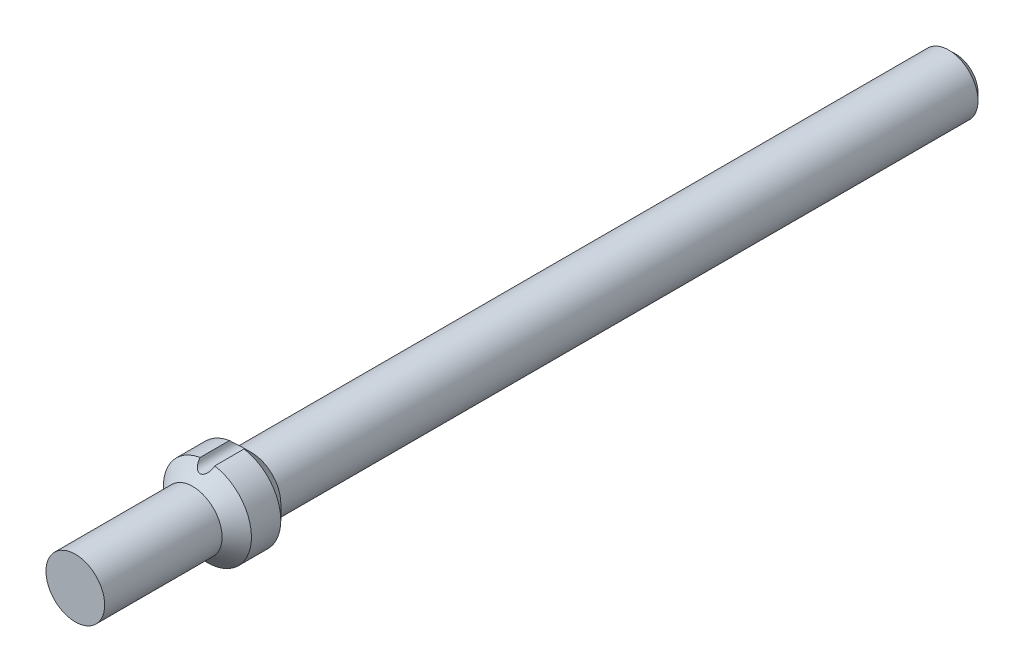
SolidWorks part; units mm, degrees
ref_plane "Front Plane" through (0, 0, 0) normal (0, 0, 1) x (1, 0, 0)
ref_plane "Top Plane" through (0, 0, 0) normal (0, 1, 0) x (1, 0, 0)
ref_plane "Right Plane" through (0, 0, 0) normal (1, 0, 0) x (0, 0, -1)
sketch "Sketch2" plane through (0, 0, 0) normal (0, 1, 0) x (1, 0, 0)
  line L0 (0, -190.5) -> (0, 190.5) construction
  line L1 (0, -190.5) -> (12.7, -190.5)
  line L2 (12.7, -190.5) -> (12.7, -139.7)
  line L3 (12.7, -139.7) -> (19.05, -133.35)
  line L4 (19.05, -133.35) -> (19.05, -120.65)
  line L5 (19.05, -120.65) -> (12.7, -114.3)
  line L6 (12.7, -114.3) -> (12.7, 187.325)
  line L7 (9.525, 190.5) -> (0, 190.5)
  line L8 (12.7, -114.3) -> (12.7, -139.7) construction
  line L9 (12.7, -127) -> (19.05, -127) construction
  line L10 (0, -190.5) -> (0, 190.5)
  line L11 (12.7, 187.325) -> (9.525, 190.5)
  point P3 (0, 0)
  point P10 (12.7, 190.5)
  point P12 (19.05, -125.053)
  dimension "D1" = 381
  dimension "D2" = 12.7
  dimension "D3" = 50.8
  dimension "D4" = 19.05
  dimension "D5" = 135
  dimension "D6" = 12.7
  dimension "D7" = 3.175
  dimension "D8" = 45
revolve "Revolve1" add sketch "Sketch2" angle 360 about L10
sketch "Sketch3" plane through (0, 0, -190.5) normal (0, 0, -1) x (-1, 0, 0)
  circle A0 centre (0, 0) radius 12.7 construction
  circle A1 centre (0, 0) radius 12.7
curve "Helix/Spiral1" [suppressed] pitch 25.4 height 304.8 turns 12
sketch "Sketch4" plane through (0, 0, 190.5) normal (0, 0, 1) x (1, 0, 0)
  circle A0 centre (0, 19.05) radius 3.175
  circle A1 centre (0, 0) radius 19.05 construction
  point P4 (0, 19.05)
  point P5 (0, 0)
  dimension "D1" = 6.35
extrude "Cut-Extrude1" cut sketch "Sketch4" against normal up to surface (69.5872 mm away)
